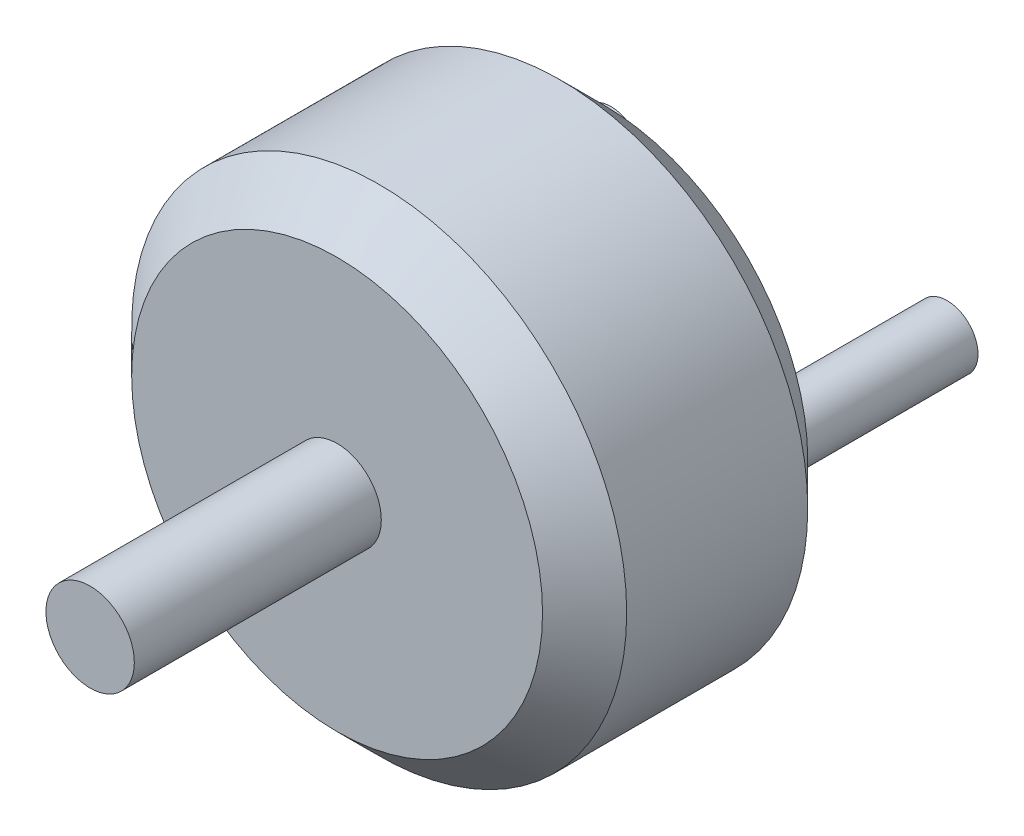
SolidWorks part; units mm, degrees
ref_plane "Front Plane" through (0, 0, 0) normal (0, 0, 1) x (1, 0, 0)
ref_plane "Top Plane" through (0, 0, 0) normal (0, 1, 0) x (1, 0, 0)
ref_plane "Right Plane" through (0, 0, 0) normal (1, 0, 0) x (0, 0, -1)
sketch "Sketch1" plane through (0, 0, 0) normal (0, 0, 1) x (1, 0, 0)
  circle A0 centre (0, 0) radius 14
  dimension "D1" = 28
extrude "Boss-Extrude1" add sketch "Sketch1" along normal blind 15
chamfer "Chamfer1" distance 2.38 angle 45 2 edges at (14, 0, 15) (14, 0, 0)
sketch "Sketch2" plane through (0, 0, 0) normal (0, 0, -1) x (-1, 0, 0)
  line L1 (6.6914, -9.5) -> (-6.6914, -9.5)
  line L2 (6.6914, -9.5) -> (6.6914, 9.5)
  line L3 (6.6914, 9.5) -> (-6.6914, 9.5)
  line L4 (-6.6914, -9.5) -> (-6.6914, 9.5)
  line L5 (6.6914, -9.5) -> (-6.6914, 9.5) construction
  line L6 (6.6914, 9.5) -> (-6.6914, -9.5) construction
  circle A0 centre (0, 0) radius 11.62 construction
  point P0 (0, 0)
  dimension "D1" = 19
sketch "Sketch3" plane through (0, 0, 15) normal (0, 0, 1) x (1, 0, 0)
  circle A0 centre (0, 0) radius 2.5
  dimension "D1" = 5
extrude "Boss-Extrude2" add sketch "Sketch3" along normal blind 13.97
ref_plane "Plane1" through (0, 0, 18.175) normal (0, 0, 1) x (1, 0, 0)
sketch "Sketch4" plane through (0, 0, 18.175) normal (0, 0, 1) x (1, 0, 0)
  circle A0 centre (0, 0) radius 76.2
  dimension "D1" = 152.4
sketch "Sketch5" plane through (0, 0, 0) normal (0, 0, -1) x (-1, 0, 0)
  circle A0 centre (-9.5, 0) radius 1.75
  circle A1 centre (9.5, 0) radius 1.75
  dimension "D1" = 3.5
  dimension "D2" = 9.5
  dimension "D3" = 2
extrude "Boss-Extrude4" add sketch "Sketch5" along normal blind 10
